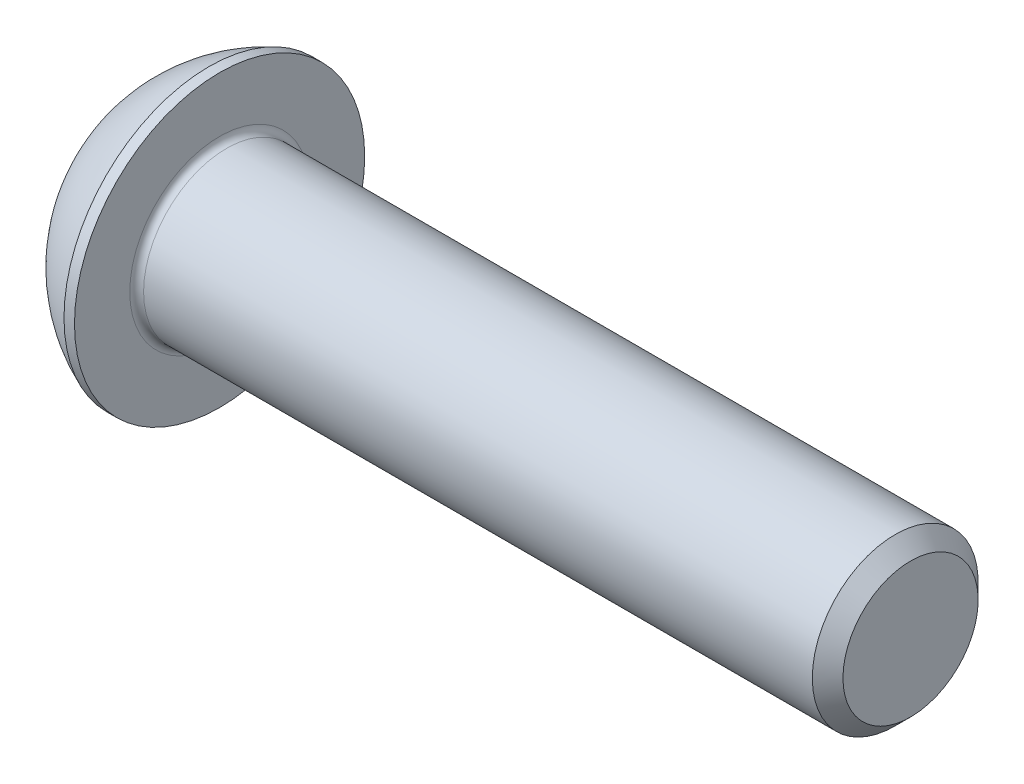
SolidWorks part; units mm, degrees
ref_plane "Plane1" through (0, 0, 0) normal (0, 0, 1) x (1, 0, 0)
ref_plane "Plane2" through (0, 0, 0) normal (0, 1, 0) x (1, 0, 0)
ref_plane "Plane3" through (0, 0, 0) normal (1, 0, 0) x (0, 0, -1)
sketch "BodySke" plane through (0, 0, 0) normal (0, 0, 1) x (1, 0, 0)
  line L0 (28.3, 0) -> (28.3, 2.4455)
  line L1 (27.7455, 3) -> (3.3, 3)
  line L2 (3.3, 3) -> (3.3, 5.25)
  line L3 (3.3, 5.25) -> (2.92, 5.25)
  line L4 (0, 0) -> (101.6, 0) construction
  line L5 (3.3, -5.25) -> (2.92, -5.25) construction
  line L6 (55.6768, -3) -> (3.3, -3) construction
  line L7 (28.3, 0) -> (0, 0)
  line L8 (0, 2.625) -> (0, -2.625) construction
  line L9 (0, 0) -> (0, 2.625)
  line L10 (28.3, 2.4455) -> (27.7455, 3)
  line L11 (28.3, -2.4455) -> (27.7455, -3) construction
  line L12 (4.3, 9.525) -> (4.3, -3) construction
  line L13 (3.3, 9.525) -> (3.3, -3) construction
  arc A1 (0, 2.625) -> (2.92, 5.25) centre (4.9997, 0) cw
  dimension "Diameter" = 6
  dimension "Length" = 25
  dimension "Head_dia" = 10.5
  dimension "D1" = 5.25
  dimension "Head_ht" = 3.3
  dimension "Head_side_ht" = 0.38
  dimension "Minor_dia" = 4.891
  dimension "Body_ch_ang" = 45
  dimension "Advance" = 1
  dimension "Thread_nom" = 25
revolve "BaseBody" add sketch "BodySke" angle 360 about L4
cosmetic thread "ThreadCosmetic" parameters "Thread_length"=23, "Thread_minor"=4.891
fillet "Fillet1" radius 0.25 1 edges at (3.3, 0, 3)
sketch "Sketch2" plane through (0, 0, 0) normal (0, 0, 1) x (1, 0, 0)
  line L0 (0, 2) -> (2.08, 2)
  line L1 (2.08, 2) -> (3.2347, 0)
  line L3 (3.2347, 0) -> (0, 0)
  line L4 (0, 0) -> (0, 2)
  line L5 (0, -2) -> (2.08, -2) construction
  line L6 (0, 0) -> (47.625, 0) construction
  dimension "D2" = 60
  dimension "PreBroach_depth" = 2.08
  dimension "PreBroach_dia" = 4
revolve "PreBroach" cut sketch "Sketch2" angle 360 about L6
sketch "Sketch3" plane through (0, 0, 0) normal (1, 0, 0) x (0, 0, -1)
  line L0 (-2, -1.1547) -> (-2, 1.1547)
  line L1 (-2, 1.1547) -> (0, 2.3094)
  line L2 (0, 2.3094) -> (2, 1.1547)
  line L3 (2, 1.1547) -> (2, -1.1547)
  line L4 (2, -1.1547) -> (0, -2.3094)
  line L5 (0, -2.3094) -> (-2, -1.1547)
  dimension "Hex_size" = 4
  dimension "D3" = 4
  dimension "D1" = 2
  dimension "D2" = 2
extrude "Hex" cut sketch "Sketch3" along normal blind 2.08
sketch "ThdSchSke" plane through (0, 0, 0) normal (0, 0, 1) x (1, 0, 0)
  line L0 (5.3, -2.4455) -> (4.9117, -3)
  line L1 (5.3, -2.4455) -> (5.6883, -3)
  line L2 (5.6883, -3) -> (5.6883, -3.75)
  line L3 (-3.175, 0) -> (5.1513, 0) construction
  line L5 (5.6883, -3.75) -> (4.9117, -3.75)
  line L6 (4.9117, -3.75) -> (4.9117, -3)
  dimension "Diameter" = 6
  dimension "Thread_minor" = 4.891
  dimension "SideAngle" = 55
  dimension "VeeAngle" = 70
  dimension "Overcut" = 7.5
  dimension "Start" = 5.3
revolve "ThreadSchematic" [suppressed] cut sketch "ThdSchSke" angle 360 about L3
pattern_linear "ThdSchPat" [suppressed]
equation "\"D1@BodySke\" = \"Head_dia@BodySke\" * .5"
equation "\"Thread_minor@ThreadCosmetic\" = \"Minor_dia@BodySke\""
equation "\"D1@Sketch3\" = \"Hex_size@Sketch3\" / 2"
equation "\"D2@Sketch3\" = \"D1@Sketch3\""
equation "\"D3@Sketch3\" = \"Hex_size@Sketch3\""
equation "\"Thread_length@ThreadCosmetic\" = ((sgn( (\"Length@BodySke\" - \"Advance@BodySke\" * 2.0) - \"Thread_nom@BodySke\" )-1)*( (\"Length@BodySke\" - \"Advance@BodySke\" * 2.0) - \"Thread_nom@BodySke\" ))/-2+ \"Thread_nom@BodySke\""
equation "\"Thread_minor@ThdSchSke\" = \"Minor_dia@BodySke\""
equation "\"Diameter@ThdSchSke\" = \"Diameter@BodySke\""
equation "\"Overcut@ThdSchSke\" = \"Diameter@BodySke\" * 1.25"
equation "\"Start@ThdSchSke\" = \"Head_ht@BodySke\" + \"Length@BodySke\" - \"Thread_length@ThreadCosmetic\"  '---Non-countersunk---"
equation "\"Num_threads@ThdSchPat\" = int( \"Thread_length@ThreadCosmetic\" / \"Advance@BodySke\" + 0.999 )  + 1"
equation "\"Advance@ThdSchPat\" = \"Thread_length@ThreadCosmetic\" /  (\"Num_threads@ThdSchPat\" - 1) 'relax it"
equation "\"Num_threads@ThdSchPat\" = \"Num_threads@ThdSchPat\" - sgn( \"Num_threads@ThdSchPat\" - 1) '---chamfered tips only---"
